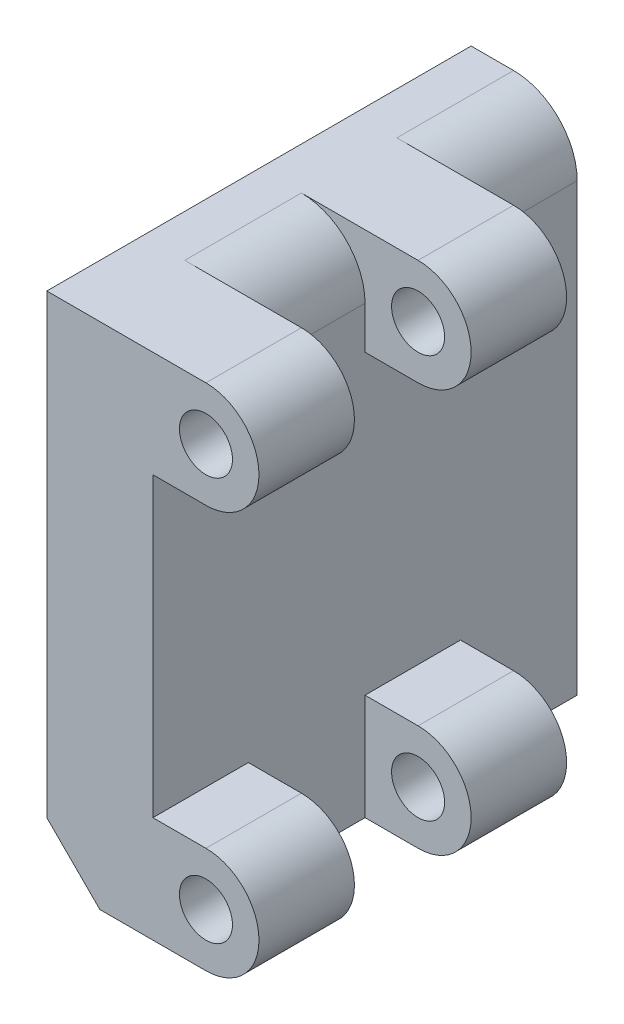
SolidWorks part; units mm, degrees
ref_plane "Front Plane" through (0, 0, 0) normal (0, 0, 1) x (1, 0, 0)
ref_plane "Top Plane" through (0, 0, 0) normal (0, 1, 0) x (1, 0, 0)
ref_plane "Right Plane" through (0, 0, 0) normal (1, 0, 0) x (0, 0, -1)
sketch "Sketch1" plane through (0, 0, 0) normal (1, 0, 0) x (0, 0, -1)
  line L1 (-20, -24) -> (20, -24)
  line L2 (-20, -24) -> (-20, 24)
  line L3 (-20, 24) -> (20, 24)
  line L4 (20, -24) -> (20, 24)
  line L5 (-20, -24) -> (20, 24) construction
  line L6 (-20, 24) -> (20, -24) construction
  point P0 (0, 0)
  dimension "D1" = 40
  dimension "D2" = 48
extrude "Boss-Extrude1" add sketch "Sketch1" along normal blind 10
sketch "Sketch6" plane through (0, 0, 20) normal (0, 0, 1) x (1, 0, 0)
  line L0 (5, 19) -> (15, 19) construction
  line L1 (10, 24) -> (10, -24) construction
  line L2 (5, 24) -> (15, 24)
  line L3 (5, 14) -> (15, 14)
  line L4 (10, 24) -> (0, 24) construction
  line L5 (10, 24) -> (10, 14.5) construction
  line L6 (10, -24.5) -> (0, -17.4979) construction
  line L7 (5, -19) -> (15, -19) construction
  line L19 (5, -14) -> (15, -14)
  line L20 (5, -24) -> (15, -24)
  line L21 (10, -24) -> (0, -24) construction
  arc A0 (5, 24) -> (5, 14) centre (5, 19) ccw
  arc A1 (15, 14) -> (15, 24) centre (15, 19) ccw
  circle A2 centre (15, 19) radius 2.5
  arc A6 (5, -14) -> (5, -24) centre (5, -19) ccw
  arc A7 (15, -24) -> (15, -14) centre (15, -19) ccw
  circle A8 centre (15, -19) radius 2.5
  point P4 (10, 19)
  point P18 (10, -19)
  dimension "D3" = 5
  dimension "D6" = 5
  dimension "D1" = 10
  dimension "D2" = 10
  dimension "D4" = 10
  dimension "D5" = 10
extrude "Boss-Extrude2" add sketch "Sketch6" against normal blind 9
pattern_linear "LPattern1" count 2 spacing 20 along (0, 0, -1) of "Boss-Extrude2"
fillet "Fillet1" radius 6 2 edges at (10, 24, -14.5) (10, 24, 5.5)
chamfer "Chamfer2" distance 5 angle 45 1 edges at (0, -24, 0)
